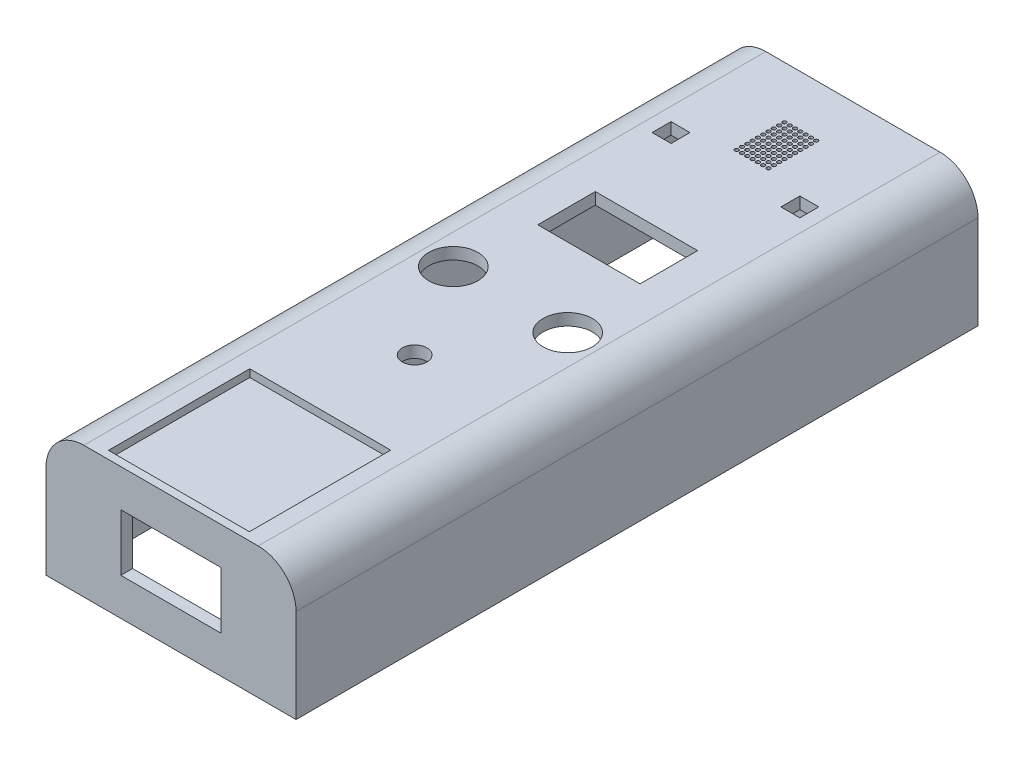
SolidWorks part; units mm, degrees
ref_plane "Front Plane" through (0, 0, 0) normal (0, 0, 1) x (1, 0, 0)
ref_plane "Top Plane" through (0, 0, 0) normal (0, 1, 0) x (1, 0, 0)
ref_plane "Right Plane" through (0, 0, 0) normal (1, 0, 0) x (0, 0, -1)
sketch "Sketch1" plane through (0, 0, 0) normal (0, 1, 0) x (1, 0, 0)
  line L1 (0, 0) -> (66, 0)
  line L2 (0, 0) -> (0, 180)
  line L3 (0, 180) -> (66, 180)
  line L4 (66, 0) -> (66, 180)
  dimension "D1" = 180
  dimension "D2" = 66
extrude "Boss-Extrude1" add sketch "Sketch1" along normal blind 34.7
sketch "Sketch2" plane through (0, 34.7, 0) normal (0, 1, 0) x (1, 0, 0)
  line L0 (33, 0) -> (33, 205.7277) construction
  line L1 (0, 0) -> (66, 0) construction
  circle A0 centre (33, 64.3) radius 3.25
  dimension "D2" = 6.5
  dimension "D1" = 64.3
sketch "Sketch3" plane through (0, 34.7, 0) normal (0, 1, 0) x (1, 0, 0)
  line L0 (33, 0) -> (33, 180) construction
  line L1 (0, 0) -> (66, 0) construction
  line L2 (66, 180) -> (0, 180) construction
  line L4 (14.4, 39.39) -> (51.6, 39.39)
  line L5 (14.4, 39.39) -> (14.4, 2.09)
  line L6 (14.4, 2.09) -> (51.6, 2.09)
  line L7 (51.6, 39.39) -> (51.6, 2.09)
  line L8 (14.4, 39.39) -> (51.6, 2.09) construction
  line L9 (14.4, 2.09) -> (51.6, 39.39) construction
  point P6 (33, 20.74)
  dimension "D1" = 37.3
  dimension "D2" = 37.2
sketch "Sketch4" plane through (0, 34.7, 0) normal (0, 1, 0) x (1, 0, 0)
  line L0 (33, 0) -> (33, 180) construction
  line L1 (0, 0) -> (66, 0) construction
  line L2 (66, 180) -> (0, 180) construction
  line L3 (0, 180) -> (0, 0) construction
  line L4 (0, 89.6) -> (66, 89.6) construction
  line L5 (66, 0) -> (66, 180) construction
  circle A0 centre (48.1, 89.6) radius 6.5
  circle A1 centre (17.9, 89.6) radius 6.5
  dimension "D2" = 13
  dimension "D3" = 13
  dimension "D1" = 89.6
  dimension "D4" = 15.1
  dimension "D5" = 15.1
sketch "Sketch5" plane through (0, 34.7, 0) normal (0, 1, 0) x (1, 0, 0)
  line L0 (33, 0) -> (33, 180) construction
  line L1 (0, 0) -> (66, 0) construction
  line L2 (66, 180) -> (0, 180) construction
  line L4 (19.5, 125.5) -> (46.5, 125.5)
  line L5 (19.5, 125.5) -> (19.5, 110.3)
  line L6 (19.5, 110.3) -> (46.5, 110.3)
  line L7 (46.5, 125.5) -> (46.5, 110.3)
  line L8 (19.5, 125.5) -> (46.5, 110.3) construction
  line L9 (19.5, 110.3) -> (46.5, 125.5) construction
  point P6 (33, 117.9)
  dimension "D1" = 15.2
  dimension "D2" = 27
  dimension "D3" = 110.3
sketch "Sketch6" plane through (0, 34.7, 0) normal (0, 1, 0) x (1, 0, 0)
  line L0 (33, 0) -> (33, 180) construction
  line L1 (0, 0) -> (66, 0) construction
  line L2 (66, 180) -> (0, 180) construction
  line L3 (0, 148.9794) -> (66, 148.9794) construction
  line L4 (27.9, 171.1486) -> (38.1, 171.1486)
  line L5 (27.9, 171.1486) -> (27.9, 158.1486)
  line L6 (27.9, 158.1486) -> (38.1, 158.1486)
  line L7 (38.1, 171.1486) -> (38.1, 158.1486)
  line L8 (27.9, 171.1486) -> (38.1, 158.1486) construction
  line L9 (27.9, 158.1486) -> (38.1, 171.1486) construction
  line L10 (0, 180) -> (0, 0) construction
  line L11 (66, 0) -> (66, 180) construction
  line L13 (47.5, 151.4794) -> (52.5, 151.4794)
  line L14 (47.5, 151.4794) -> (47.5, 146.4794)
  line L15 (47.5, 146.4794) -> (52.5, 146.4794)
  line L16 (52.5, 151.4794) -> (52.5, 146.4794)
  line L17 (47.5, 151.4794) -> (52.5, 146.4794) construction
  line L18 (47.5, 146.4794) -> (52.5, 151.4794) construction
  line L19 (18.5, 146.4794) -> (13.5, 146.4794)
  line L20 (13.5, 151.4794) -> (13.5, 146.4794)
  line L21 (18.5, 151.4794) -> (13.5, 151.4794)
  line L22 (18.5, 151.4794) -> (18.5, 146.4794)
  point P6 (33, 164.6486)
  point P17 (50, 148.9794)
  dimension "D1" = 13
  dimension "D2" = 10.2
  dimension "D3" = 5
  dimension "D4" = 5
  dimension "D5" = 17
sketch "Sketch20" plane through (0, 34.7, 0) normal (0, 1, 0) x (1, 0, 0)
  line L0 (33, 180) -> (33, 119.0875) construction
  line L1 (66, 180) -> (0, 180) construction
  line L3 (27.9, 153.2735) -> (38.1, 153.2735)
  line L4 (27.9, 153.2735) -> (27.9, 167.2735)
  line L5 (27.9, 167.2735) -> (38.1, 167.2735)
  line L6 (38.1, 153.2735) -> (38.1, 167.2735)
  line L7 (27.9, 153.2735) -> (38.1, 167.2735) construction
  line L8 (27.9, 167.2735) -> (38.1, 153.2735) construction
  point P4 (33, 160.2735)
  dimension "D1" = 14
  dimension "D2" = 10.2
fillet "Fillet1" radius 10 2 edges at (66, 34.7, -90) (0, 34.7, -90)
shell "Shell1" thickness 3.1
extrude "Cut-Extrude4" cut sketch "Sketch4" against normal through all contours A0 | A1
extrude "Cut-Extrude5" cut sketch "Sketch2" against normal through all contours A0
extrude "Cut-Extrude6" cut sketch "Sketch5" against normal through all contours L7 L6 L5 L4
extrude "Cut-Extrude10" cut sketch "Sketch6" against normal through all contours L15 L16 L13 L14 | L19 L20 L21 L22
sketch "Sketch31" plane through (0, 34.7, 0) normal (0, 1, 0) x (1, 0, 0)
  line L0 (27.9, 167.2735) -> (38.1, 153.2735) construction
  line L1 (27.9, 167.2735) -> (38.1, 167.2735) construction
  line L2 (27.9, 153.2735) -> (27.9, 167.2735) construction
  circle A0 centre (28.6286, 166.2735) radius 0.5
  circle A1 centre (30.0286, 166.2735) radius 0.5
  circle A2 centre (31.4286, 166.2735) radius 0.5
  circle A3 centre (32.8286, 166.2735) radius 0.5
  circle A4 centre (34.2286, 166.2735) radius 0.5
  circle A5 centre (35.6286, 166.2735) radius 0.5
  circle A6 centre (37.0286, 166.2735) radius 0.5
  circle A7 centre (30.0286, 164.8735) radius 0.5
  circle A8 centre (31.4286, 164.8735) radius 0.5
  circle A9 centre (32.8286, 164.8735) radius 0.5
  circle A10 centre (34.2286, 164.8735) radius 0.5
  circle A11 centre (35.6286, 164.8735) radius 0.5
  circle A12 centre (37.0286, 164.8735) radius 0.5
  circle A13 centre (30.0286, 163.4735) radius 0.5
  circle A14 centre (31.4286, 163.4735) radius 0.5
  circle A15 centre (32.8286, 163.4735) radius 0.5
  circle A16 centre (34.2286, 163.4735) radius 0.5
  circle A17 centre (35.6286, 163.4735) radius 0.5
  circle A18 centre (37.0286, 163.4735) radius 0.5
  circle A19 centre (30.0286, 162.0735) radius 0.5
  circle A20 centre (31.4286, 162.0735) radius 0.5
  circle A21 centre (32.8286, 162.0735) radius 0.5
  circle A22 centre (34.2286, 162.0735) radius 0.5
  circle A23 centre (35.6286, 162.0735) radius 0.5
  circle A24 centre (37.0286, 162.0735) radius 0.5
  circle A25 centre (30.0286, 160.6735) radius 0.5
  circle A26 centre (31.4286, 160.6735) radius 0.5
  circle A27 centre (32.8286, 160.6735) radius 0.5
  circle A28 centre (34.2286, 160.6735) radius 0.5
  circle A29 centre (35.6286, 160.6735) radius 0.5
  circle A30 centre (37.0286, 160.6735) radius 0.5
  circle A31 centre (30.0286, 159.2735) radius 0.5
  circle A32 centre (31.4286, 159.2735) radius 0.5
  circle A33 centre (32.8286, 159.2735) radius 0.5
  circle A34 centre (34.2286, 159.2735) radius 0.5
  circle A35 centre (35.6286, 159.2735) radius 0.5
  circle A36 centre (37.0286, 159.2735) radius 0.5
  circle A37 centre (30.0286, 157.8735) radius 0.5
  circle A38 centre (31.4286, 157.8735) radius 0.5
  circle A39 centre (32.8286, 157.8735) radius 0.5
  circle A40 centre (34.2286, 157.8735) radius 0.5
  circle A41 centre (35.6286, 157.8735) radius 0.5
  circle A42 centre (37.0286, 157.8735) radius 0.5
  circle A43 centre (30.0286, 156.4735) radius 0.5
  circle A44 centre (31.4286, 156.4735) radius 0.5
  circle A45 centre (32.8286, 156.4735) radius 0.5
  circle A46 centre (34.2286, 156.4735) radius 0.5
  circle A47 centre (35.6286, 156.4735) radius 0.5
  circle A48 centre (37.0286, 156.4735) radius 0.5
  circle A49 centre (30.0286, 155.0735) radius 0.5
  circle A50 centre (31.4286, 155.0735) radius 0.5
  circle A51 centre (32.8286, 155.0735) radius 0.5
  circle A52 centre (34.2286, 155.0735) radius 0.5
  circle A53 centre (35.6286, 155.0735) radius 0.5
  circle A54 centre (37.0286, 155.0735) radius 0.5
  circle A55 centre (30.0286, 153.6735) radius 0.5
  circle A56 centre (31.4286, 153.6735) radius 0.5
  circle A57 centre (32.8286, 153.6735) radius 0.5
  circle A58 centre (34.2286, 153.6735) radius 0.5
  circle A59 centre (35.6286, 153.6735) radius 0.5
  circle A60 centre (37.0286, 153.6735) radius 0.5
  circle A61 centre (28.6286, 164.8735) radius 0.5
  circle A62 centre (28.6286, 163.4735) radius 0.5
  circle A63 centre (28.6286, 162.0735) radius 0.5
  circle A64 centre (28.6286, 160.6735) radius 0.5
  circle A65 centre (28.6286, 159.2735) radius 0.5
  circle A66 centre (28.6286, 157.8735) radius 0.5
  circle A67 centre (28.6286, 156.4735) radius 0.5
  circle A68 centre (28.6286, 155.0735) radius 0.5
  circle A69 centre (28.6286, 153.6735) radius 0.5
  dimension "D1" = 1
  dimension "D2" = 1
  dimension "D3" = 0.7286
  dimension "D4" = 7
  dimension "D5" = 10
extrude "Cut-Extrude11" cut sketch "Sketch31" against normal through all
sketch "Sketch32" plane through (0, 0, 0) normal (0, 0, 1) x (1, 0, 0)
  line L0 (33, 0) -> (33, 34.7)
  line L1 (0, 0) -> (66, 0) construction
  line L3 (19.75, 24.85) -> (46.25, 24.85)
  line L4 (19.75, 24.85) -> (19.75, 9.85)
  line L5 (19.75, 9.85) -> (46.25, 9.85)
  line L6 (46.25, 24.85) -> (46.25, 9.85)
  line L7 (19.75, 24.85) -> (46.25, 9.85) construction
  line L8 (19.75, 9.85) -> (46.25, 24.85) construction
  point P5 (33, 17.35)
  point P10 (0, 0)
  point P11 (0, 0)
  point P12 (0, 0)
  dimension "D1" = 26.5
  dimension "D2" = 15
extrude "Cut-Extrude14" cut sketch "Sketch3" against normal blind 2 contours L5 L6 L7 L4
extrude "Cut-Extrude16" cut sketch "Sketch32" against normal blind 5 contours L3 L6 L5 L4
